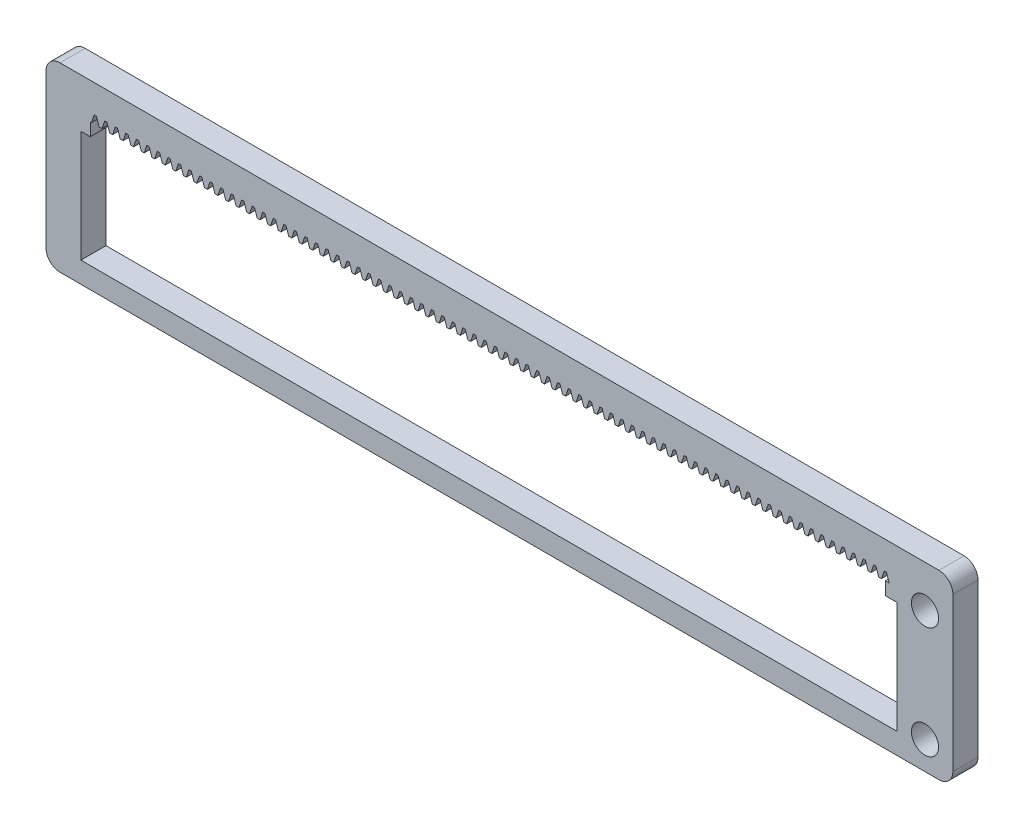
SolidWorks part; units mm, degrees
ref_plane "Front Plane" through (0, 0, 0) normal (0, 0, 1) x (1, 0, 0)
ref_plane "Top Plane" through (0, 0, 0) normal (0, 1, 0) x (1, 0, 0)
ref_plane "Right Plane" through (0, 0, 0) normal (1, 0, 0) x (0, 0, -1)
sketch "Sketch1" plane through (0, 0, 0) normal (0, 0, 1) x (1, 0, 0)
  line L1 (2, 0) -> (128, 0)
  line L2 (0, -2) -> (0, -24)
  line L3 (2, -26) -> (128, -26)
  line L4 (130, -2) -> (130, -24)
  arc A0 (128, -26) -> (130, -24) centre (128, -24) ccw
  arc A1 (0, -24) -> (2, -26) centre (2, -24) ccw
  arc A2 (2, 0) -> (0, -2) centre (2, -2) ccw
  arc A3 (128, 0) -> (130, -2) centre (128, -2) cw
  point P7 (130, -26)
  point P12 (0, 0)
  point P15 (130, 0)
  dimension "D3" = 2
  dimension "D1" = 26
  dimension "D2" = 130
extrude "Boss-Extrude1" add sketch "Sketch1" along normal blind 3.6
sketch "Sketch2" plane through (0, 0, 3.6) normal (0, 0, 1) x (1, 0, 0)
  line L1 (5, -7) -> (122, -7)
  line L2 (5, -7) -> (5, -23)
  line L3 (5, -23) -> (122, -23)
  line L4 (122, -7) -> (122, -23)
  line L5 (0, -2) -> (0, -24) construction
  line L7 (130, -24) -> (130, -2) construction
  line L8 (5, -15) -> (122, -15) construction
  line L11 (2, -26) -> (128, -26) construction
  dimension "D1" = 16
  dimension "D2" = 8
  dimension "D3" = 5
  dimension "D4" = 3
extrude "Cut-Extrude1" cut sketch "Sketch2" against normal blind 3.6
sketch "Sketch3" plane through (0, 0, 3.6) normal (0, 0, 1) x (1, 0, 0)
  line L0 (122, -7) -> (5, -7) construction
  line L1 (6.35, -7) -> (120.32, -7)
  line L2 (6.35, -7) -> (6.35, -5.15)
  line L3 (6.35, -5.15) -> (120.32, -5.15)
  line L4 (120.32, -7) -> (120.32, -5.15)
  line L5 (122, -23) -> (122, -7) construction
  line L6 (5, -7) -> (5, -23) construction
  dimension "D1" = 1.85
  dimension "D2" = 1.68
  dimension "D3" = 1.35
extrude "Cut-Extrude2" cut sketch "Sketch3" against normal blind 3.6
sketch "Sketch4" plane through (0, 0, 3.6) normal (0, 0, 1) x (1, 0, 0)
  line L0 (121.345, -5.15) -> (120.865, -5.15) construction
  line L1 (120.32, -5.15) -> (6.35, -5.15) construction
  line L2 (121.345, -5.15) -> (121.725, -4.0118) construction
  line L3 (121.725, -4.0118) -> (120.485, -4.0118) construction
  line L4 (120.485, -4.0118) -> (120.865, -5.15)
  line L5 (120.485, -4.0118) -> (120.155, -4.0118)
  line L6 (120.155, -4.0118) -> (119.775, -5.15)
  line L7 (119.775, -5.15) -> (120.865, -5.15)
  line L10 (120.865, -5.15) -> (121.345, -5.15) construction
  dimension "D1" = 0.48
  dimension "D2" = 1.2
  dimension "D3" = 1.2
  dimension "D4" = 0.33
  dimension "D5" = 1.24
  dimension "D6" = 1.2
extrude "Cut-Extrude4" cut sketch "Sketch4" against normal blind 3.6
pattern_linear "LPattern1" count 76 spacing 1.51 along (-1, 0, 0) of "Cut-Extrude4"
sketch "Sketch5" plane through (0, 0, 3.6) normal (0, 0, 1) x (1, 0, 0)
  line L1 (128, 0) -> (2, 0) construction
  line L3 (130, -24) -> (130, -2) construction
  circle A1 centre (126, -6) radius 1.95
  circle A3 centre (126, -22) radius 1.95
  dimension "D1" = 3.9
  dimension "D4" = 3.9
  dimension "D5" = 4
  dimension "D6" = 4
  dimension "D7" = 6
  dimension "D9" = 16
extrude "Cut-Extrude5" cut sketch "Sketch5" against normal blind 10
